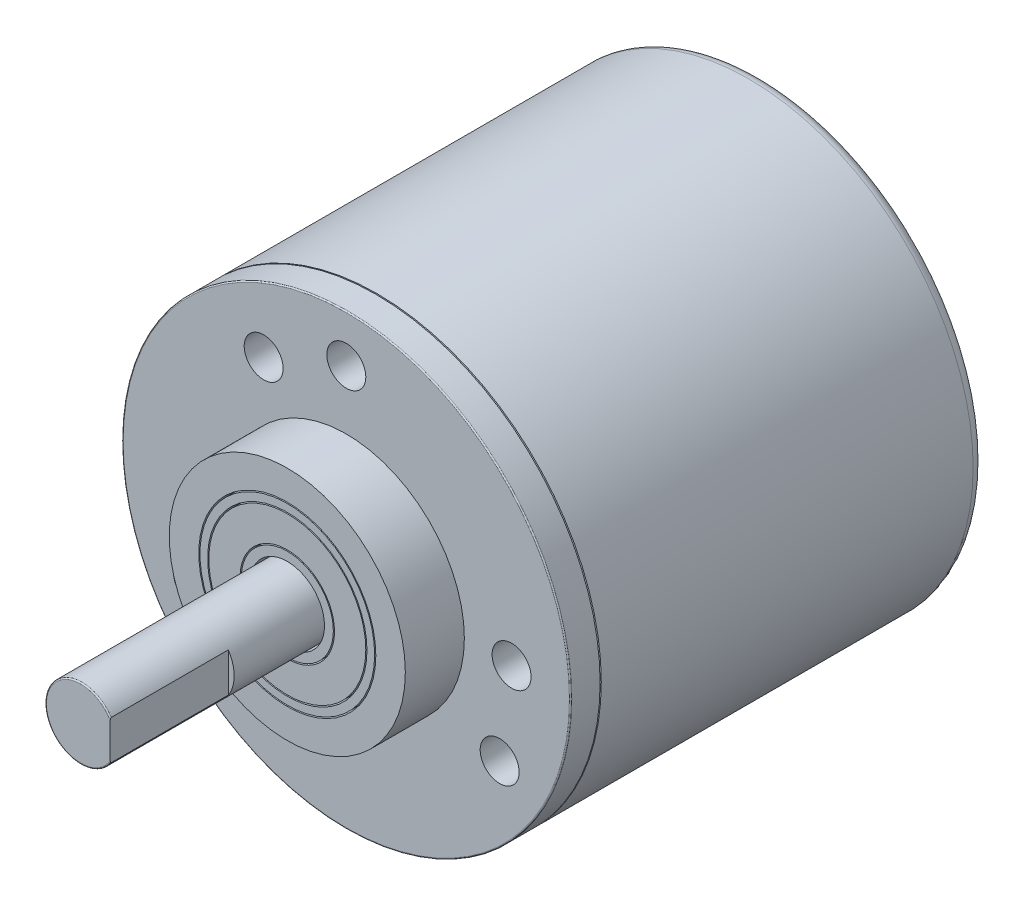
SolidWorks part; units mm, degrees
ref_plane "Front Plane" through (0, 0, 0) normal (0, 0, 1) x (1, 0, 0)
ref_plane "Top Plane" through (0, 0, 0) normal (0, 1, 0) x (1, 0, 0)
ref_plane "Right Plane" through (0, 0, 0) normal (1, 0, 0) x (0, 0, -1)
sketch "Sketch1" plane through (0, 0, 0) normal (0, 0, 1) x (1, 0, 0)
  circle A0 centre (0, 0) radius 19
  dimension "D1" = 38
extrude "Boss-Extrude1" add sketch "Sketch1" along normal blind 32.5
sketch "Sketch2" plane through (0, 0, 32.5) normal (0, 0, 1) x (1, 0, 0)
  circle A0 centre (0, 0) radius 18.5
  dimension "D1" = 37
extrude "Boss-Extrude2" add sketch "Sketch2" along normal blind 0.1
sketch "Sketch3" plane through (0, 0, 32.6) normal (0, 0, 1) x (1, 0, 0)
  circle A0 centre (0, 0) radius 19
  dimension "D1" = 38
extrude "Boss-Extrude3" add sketch "Sketch3" along normal blind 2.5
sketch "Sketch4" plane through (0, 0, 35.1) normal (0, 0, 1) x (1, 0, 0)
  circle A0 centre (0, 0) radius 10
  dimension "D1" = 20
extrude "Boss-Extrude4" add sketch "Sketch4" along normal blind 5
sketch "Sketch5" plane through (0, 0, 40.1) normal (0, 0, 1) x (1, 0, 0)
  circle A0 centre (0, 0) radius 7.5
  dimension "D1" = 15
extrude "Cut-Extrude1" cut sketch "Sketch5" against normal blind 3
sketch "Sketch6" plane through (0, 0, 37.1) normal (0, 0, 1) x (1, 0, 0)
  circle A0 centre (0, 0) radius 7.4
  circle A1 centre (0, 0) radius 6.75
  dimension "D1" = 13.5
  dimension "D2" = 14.8
extrude "Boss-Extrude6" add sketch "Sketch6" along normal blind 3
sketch "Sketch7" plane through (0, 0, 37.1) normal (0, 0, 1) x (1, 0, 0)
  circle A0 centre (0, 0) radius 6.65
  circle A1 centre (0, 0) radius 4
  dimension "D1" = 13.3
  dimension "D2" = 8
extrude "Boss-Extrude7" add sketch "Sketch7" along normal blind 3
sketch "Sketch8" plane through (0, 0, 37.1) normal (0, 0, 1) x (1, 0, 0)
  circle A0 centre (0, 0) radius 3.9
  circle A1 centre (0, 0) radius 3.15
  dimension "D1" = 7.8
  dimension "D2" = 6.3
extrude "Boss-Extrude8" add sketch "Sketch8" along normal blind 3
sketch "Sketch9" plane through (0, 0, 37.1) normal (0, 0, 1) x (1, 0, 0)
  circle A0 centre (0, 0) radius 3
  dimension "D1" = 6
extrude "Boss-Extrude9" add sketch "Sketch9" along normal blind 20.5
ref_plane "Plane1" through (3, 0, 0) normal (1, 0, 0) x (0, 0, -1)
sketch "Sketch11" plane through (3, 0, 0) normal (1, 0, 0) x (0, 0, -1)
  line L0 (-37.1, 3) -> (-57.6, 3) construction
  line L1 (-57.6, -3) -> (-47.6, -3)
  line L2 (-57.6, -3) -> (-57.6, 3)
  line L3 (-57.6, 3) -> (-47.6, 3)
  line L4 (-47.6, -3) -> (-47.6, 3)
  dimension "D1" = 10
extrude "Cut-Extrude2" cut sketch "Sketch11" against normal blind 0.5
fillet "Fillet1" radius 0.1 1 edges at (-3, 0, 57.6)
fillet "Fillet2" radius 0.1 1 edges at (19, 0, 35.1)
fillet "Fillet3" radius 1 1 edges at (19, 0, 0)
sketch "Sketch12" plane through (0, 0, 35.1) normal (0, 0, 1) x (1, 0, 0)
  line L0 (0, 0) -> (0, 15) construction
  line L1 (0, 0) -> (12.9904, -7.5) construction
  line L2 (-7, 12.1244) -> (0, 0) construction
  circle A0 centre (0, 0) radius 15 construction
  circle A1 centre (0, 15) radius 1.25
  circle A2 centre (12.9904, -7.5) radius 1.25
  circle A3 centre (-12.9904, -7.5) radius 1.25
  circle A4 centre (0, 0) radius 14 construction
  circle A5 centre (-7, 12.1244) radius 1.25
  circle A6 centre (14, 0) radius 1.25
  circle A7 centre (-7, -12.1244) radius 1.25
  dimension "D1" = 30
  dimension "D2" = 2.5
  dimension "D5" = 28
  dimension "D6" = 2.5
  dimension "D7" = 3
  dimension "D4" = 120
  dimension "D8" = 30
  dimension "D3" = 3
hole_wizard "M4 Tapped Hole1" positions "3DSketch1" profile "Sketch13" tap size "M4" standard "ISO"
sketch3d "3DSketch1"
  point P0 (-7, 12.1244, 35.1)
  point P3 (0, 15, 35.1)
  point P6 (14, 0, 35.1)
  point P9 (12.9904, -7.5, 35.1)
  point P12 (-7, -12.1244, 35.1)
  point P15 (-12.9904, -7.5, 35.1)
cosmetic thread "Hole Thread1" parameters "D1"=5, "D2"=4
cosmetic thread "Hole Thread2" parameters "D1"=5, "D2"=4
cosmetic thread "Hole Thread3" parameters "D1"=5, "D2"=4
cosmetic thread "Hole Thread4" parameters "D1"=5, "D2"=4
cosmetic thread "Hole Thread5" parameters "D1"=5, "D2"=4
cosmetic thread "Hole Thread6" parameters "D1"=5, "D2"=4
sketch "Sketch13" plane through (-7, 12.1244, 35.1) normal (1, 0, 0) x (0, -1, 0)
  line L0 (0, 0) -> (0, 5.9914)
  line L1 (0, 5.9914) -> (1.65, 5)
  line L2 (1.65, 5) -> (1.65, 0)
  line L5 (1.65, 0) -> (0, 0)
  line L10 (0, 5.9914) -> (-1.65, 5) construction
  line L11 (0, -6.35) -> (0, 107.95) construction
  dimension "Tap Drill Dia." = 3.3
  dimension "Tap Drill Depth" = 5
  dimension "Drill Angle" = 118
